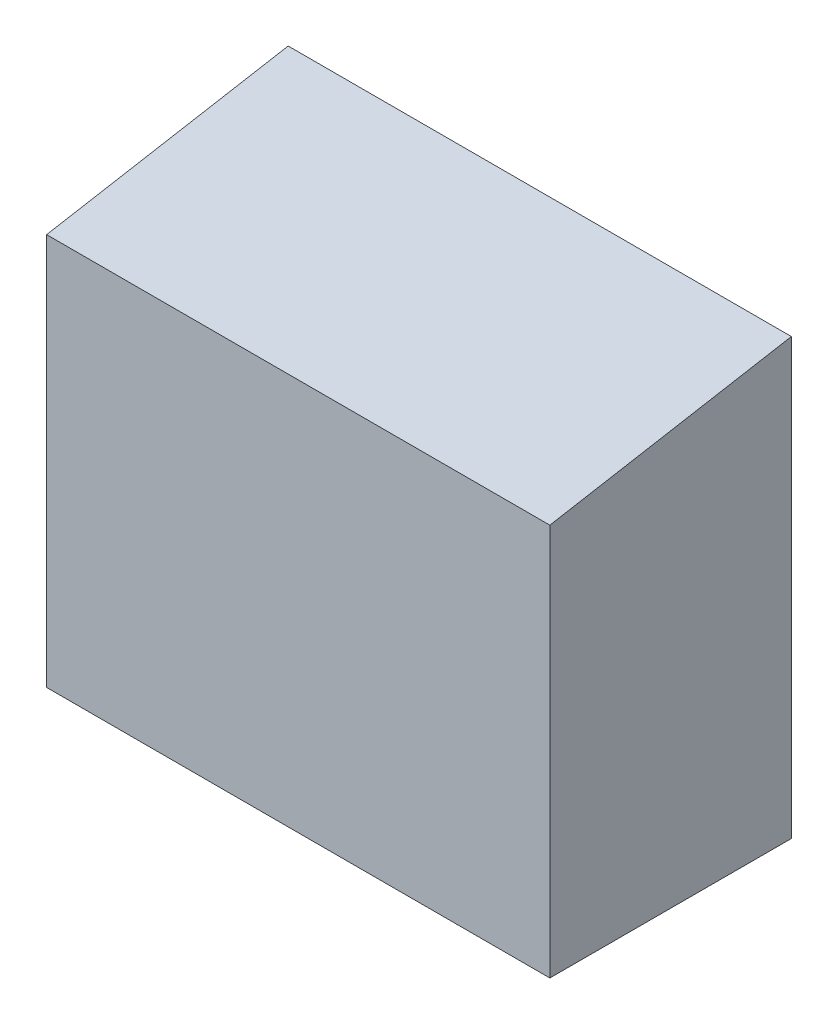
SolidWorks part; units mm, degrees
material "ABS"
ref_plane "Front Plane" through (0, 0, 0) normal (0, 0, 1) x (1, 0, 0)
ref_plane "Top Plane" through (0, 0, 0) normal (0, 1, 0) x (1, 0, 0)
ref_plane "Right Plane" through (0, 0, 0) normal (1, 0, 0) x (0, 0, -1)
sketch "Sketch3" plane through (0, 0, 0) normal (1, 0, 0) x (0, 0, -1)
  line L0 (0, 0) -> (38.1, 0)
  line L1 (38.1, 0) -> (38.1, 68.58)
  line L2 (38.1, 68.58) -> (0, 61.8619)
  line L3 (0, 61.8619) -> (0, 0)
  dimension "D1" = 10
  dimension "D2" = 68.58
  dimension "D3" = 38.1
extrude "Boss-Extrude2" add sketch "Sketch3" along normal mid plane 79.375
sketch "Sketch4" plane through (0, 0, 0) normal (0, -1, 0) x (1, 0, 0)
  line L0 (-39.6875, -19.05) -> (39.6875, -19.05) construction
  line L1 (-39.6875, 0) -> (-39.6875, -38.1) construction
  line L2 (39.6875, 0) -> (39.6875, -38.1) construction
  line L3 (0, 0) -> (0, -38.1) construction
  line L4 (39.6875, -38.1) -> (-39.6875, -38.1) construction
  point P6 (-25.4, -19.05)
  point P12 (25.4, -19.05)
  dimension "D1" = 25.4
hole_wizard "1/4-20 Tapped Hole1" positions "Sketch5" profile "Sketch6" tap size "1/4-20" standard "ANSI Inch"
sketch "Sketch5" plane through (0, 0, 0) normal (0, -1, 0) x (-1, 0, 0)
  point P0 (25.4, 19.05)
  point P3 (-25.4, 19.05)
sketch "Sketch6" plane through (-25.4, 0, -19.05) normal (1, 0, 0) x (0, 0, -1)
  line L0 (0, 0) -> (0, 24.3938)
  line L1 (0, 24.3938) -> (2.5527, 22.86)
  line L2 (2.5527, 22.86) -> (2.5527, 0)
  line L5 (2.5527, 0) -> (0, 0)
  line L10 (0, 24.3938) -> (-2.5527, 22.86) construction
  line L11 (0, -6.35) -> (0, 107.95) construction
  dimension "Tap Drill Dia." = 5.1054
  dimension "Tap Drill Depth" = 22.86
  dimension "Drill Angle" = 118
cosmetic thread "Hole Thread1" parameters "D1"=19.05, "D2"=6.35
cosmetic thread "Hole Thread2" parameters "D1"=19.05, "D2"=6.35
sketch "Sketch7" plane through (0, 59.9966, 10.579) normal (0, 0.9848, 0.1736) x (1, 0, 0)
  line L0 (-39.6875, 32.285) -> (39.6875, 32.285) construction
  line L1 (-39.6875, 49.43) -> (-39.6875, 10.7422) construction
  line L2 (39.6875, 49.43) -> (39.6875, 10.7422) construction
  line L3 (0, 10.7422) -> (0, 49.43) construction
  line L4 (39.6875, 10.7422) -> (-39.6875, 10.7422) construction
  line L5 (39.6875, 49.43) -> (-39.6875, 49.43) construction
  point P6 (-25.4, 32.285)
  point P7 (25.4, 32.285)
  dimension "D1" = 50.8
  dimension "D2" = 17.145
hole_wizard "#8-32 Tapped Hole1" [suppressed] positions "Sketch8" profile "Sketch9" tap size "#8-32" standard "ANSI Inch"
sketch "Sketch8" plane through (0, 59.9966, 10.579) normal (0, 0.9848, 0.1736) x (1, 0, 0)
  point P0 (-25.4, 32.285)
  point P3 (25.4, 32.285)
sketch "Sketch9" plane through (-25.4, 65.6028, -21.2155) normal (1, 0, 0) x (0, -0.1736, 0.9848)
  line L0 (0, 0) -> (0, 16.0238)
  line L1 (0, 16.0238) -> (1.7272, 14.986)
  line L2 (1.7272, 14.986) -> (1.7272, 0)
  line L5 (1.7272, 0) -> (0, 0)
  line L10 (0, 16.0238) -> (-1.7272, 14.986) construction
  line L11 (0, -6.35) -> (0, 107.95) construction
  dimension "Tap Drill Dia." = 3.4544
  dimension "Tap Drill Depth" = 14.986
  dimension "Drill Angle" = 118
cosmetic thread "Hole Thread3" [suppressed] parameters "D1"=12.7, "D2"=4.1656
cosmetic thread "Hole Thread4" [suppressed] parameters "D1"=12.7, "D2"=4.1656
